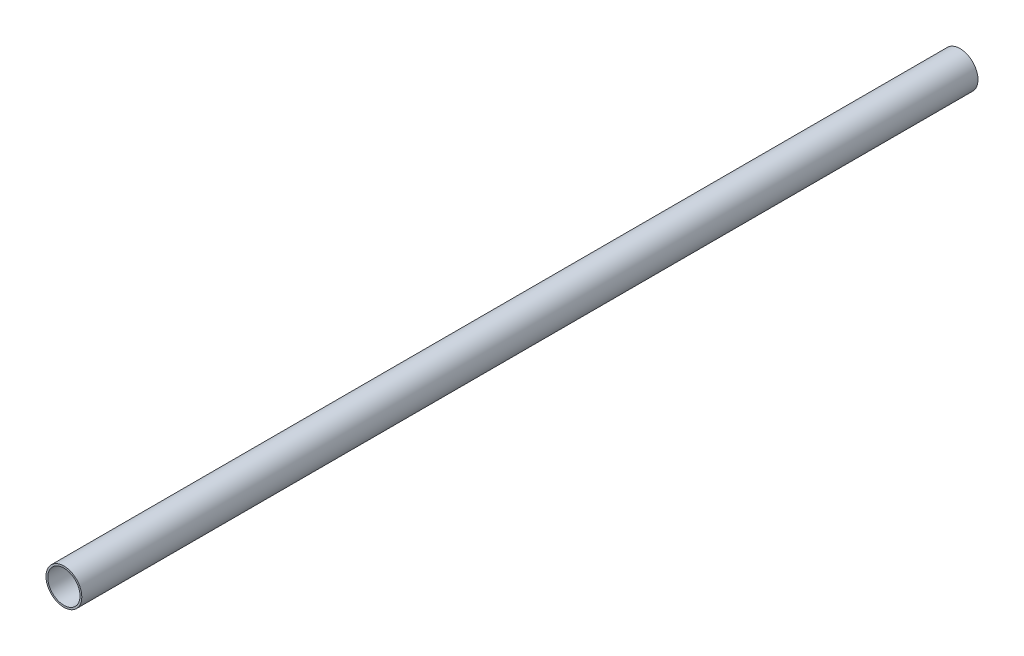
SolidWorks part; units mm, degrees
material "Thornel Mat VMA"
ref_plane "Front Plane" through (0, 0, 0) normal (0, 0, 1) x (1, 0, 0)
ref_plane "Top Plane" through (0, 0, 0) normal (0, 1, 0) x (1, 0, 0)
ref_plane "Right Plane" through (0, 0, 0) normal (1, 0, 0) x (0, 0, -1)
sketch "Sketch1" plane through (0, 0, 0) normal (0, 0, 1) x (1, 0, 0)
  circle A0 centre (0, 0) radius 9
  circle A1 centre (0, 0) radius 10
  dimension "D1" = 20
  dimension "D2" = 18
extrude "Boss-Extrude1" add sketch "Sketch1" along normal blind 500
